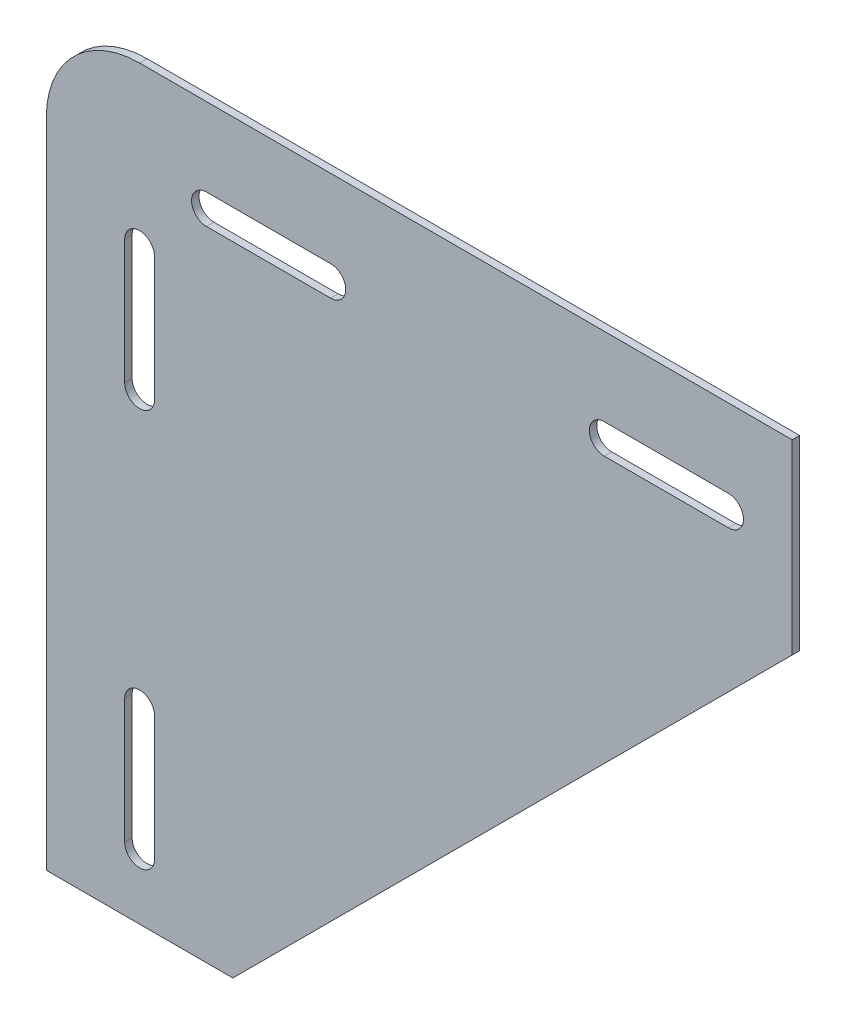
SolidWorks part; units mm, degrees
ref_plane "Front Plane" through (0, 0, 0) normal (0, 0, 1) x (1, 0, 0)
ref_plane "Top Plane" through (0, 0, 0) normal (0, 1, 0) x (1, 0, 0)
ref_plane "Right Plane" through (0, 0, 0) normal (1, 0, 0) x (0, 0, -1)
sketch "Sketch1" plane through (0, 0, 0) normal (0, 0, 1) x (1, 0, 0)
  line L0 (0, -76.2) -> (0, -9.525)
  line L1 (9.525, 0) -> (76.2, 0)
  line L2 (76.2, 0) -> (76.2, -19.05)
  line L3 (76.2, -19.05) -> (19.05, -76.2)
  line L4 (19.05, -76.2) -> (0, -76.2)
  line L5 (56.9976, -9.525) -> (69.6976, -9.525) construction
  line L6 (56.9976, -8.001) -> (69.6976, -8.001)
  line L7 (56.9976, -11.049) -> (69.6976, -11.049)
  line L8 (9.525, -9.525) -> (47.625, -47.625) construction
  line L9 (9.525, -56.9976) -> (9.525, -69.6976) construction
  line L10 (8.001, -56.9976) -> (8.001, -69.6976)
  line L11 (11.049, -56.9976) -> (11.049, -69.6976)
  line L12 (29.0576, -9.525) -> (16.3576, -9.525) construction
  line L13 (29.0576, -11.049) -> (16.3576, -11.049)
  line L14 (29.0576, -8.001) -> (16.3576, -8.001)
  line L15 (9.525, -29.0576) -> (9.525, -16.3576) construction
  line L16 (11.049, -29.0576) -> (11.049, -16.3576)
  line L17 (8.001, -29.0576) -> (8.001, -16.3576)
  arc A0 (0, -9.525) -> (9.525, 0) centre (9.525, -9.525) cw
  arc A1 (56.9976, -8.001) -> (56.9976, -11.049) centre (56.9976, -9.525) ccw
  arc A2 (69.6976, -11.049) -> (69.6976, -8.001) centre (69.6976, -9.525) ccw
  arc A3 (8.001, -56.9976) -> (11.049, -56.9976) centre (9.525, -56.9976) cw
  arc A4 (11.049, -69.6976) -> (8.001, -69.6976) centre (9.525, -69.6976) cw
  arc A5 (29.0576, -11.049) -> (29.0576, -8.001) centre (29.0576, -9.525) ccw
  arc A6 (16.3576, -8.001) -> (16.3576, -11.049) centre (16.3576, -9.525) ccw
  arc A7 (11.049, -29.0576) -> (8.001, -29.0576) centre (9.525, -29.0576) cw
  arc A8 (8.001, -16.3576) -> (11.049, -16.3576) centre (9.525, -16.3576) cw
  point P8 (0, 0)
  point P11 (63.3476, -9.525)
  point P19 (9.525, -63.3476)
  point P26 (22.7076, -9.525)
  point P33 (9.525, -22.7076)
  dimension "D3" = 9.525
  dimension "D4" = 1.524
  dimension "D1" = 19.05
  dimension "D2" = 76.2
  dimension "D5" = 6.5024
  dimension "D6" = 9.525
  dimension "D7" = 12.7
  dimension "D8" = 40.64
extrude "Boss-Extrude1" add sketch "Sketch1" along normal blind 0.762
